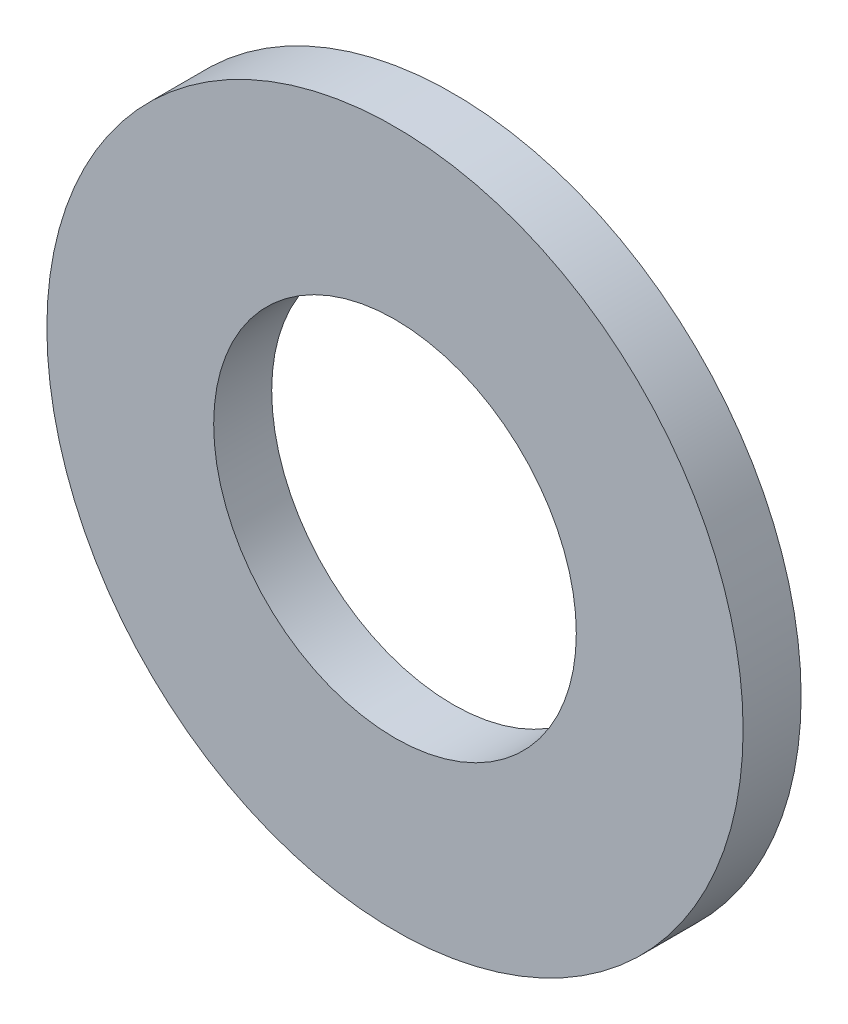
SolidWorks part; units mm, degrees
ref_plane "Front Plane" through (0, 0, 0) normal (0, 0, 1) x (1, 0, 0)
ref_plane "Top Plane" through (0, 0, 0) normal (0, 1, 0) x (1, 0, 0)
ref_plane "Right Plane" through (0, 0, 0) normal (1, 0, 0) x (0, 0, -1)
sketch "Sketch2" plane through (0, 0, 0) normal (0, 0, 1) x (1, 0, 0)
  circle A0 centre (0, 0) radius 6
  circle A1 centre (0, 0) radius 3.125
extrude "Boss-Extrude1" add sketch "Sketch2" along normal blind 1
